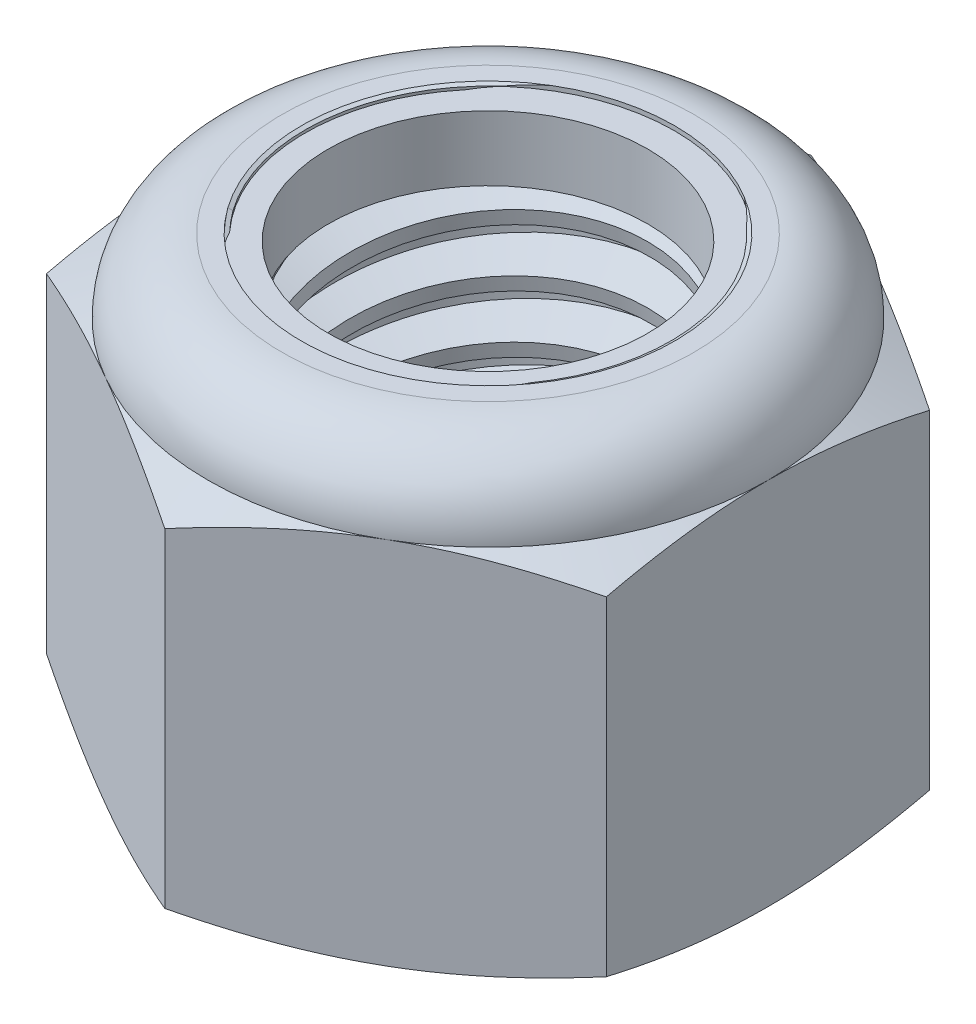
SolidWorks part; units mm, degrees
material "Plain Carbon Steel"
ref_plane "Front" through (0, 0, 0) normal (0, 0, 1) x (1, 0, 0)
ref_plane "Top" through (0, 0, 0) normal (0, 1, 0) x (1, 0, 0)
ref_plane "Right" through (0, 0, 0) normal (1, 0, 0) x (0, 0, -1)
sketch "Sketch1" plane through (0, 0, 0) normal (0, 1, 0) x (1, 0, 0)
  line L1 (0, 10.9985) -> (-9.525, 5.4993)
  line L2 (-9.525, 5.4993) -> (-9.525, -5.4993)
  line L3 (-9.525, -5.4993) -> (0, -10.9985)
  line L4 (0, -10.9985) -> (9.525, -5.4993)
  line L5 (9.525, -5.4993) -> (9.525, 5.4993)
  line L6 (9.525, 5.4993) -> (0, 10.9985)
  circle A0 centre (0, 0) radius 9.525 construction
  dimension "Hex Flats" = 19.05
extrude "Extrude1" add sketch "Sketch1" along normal blind 15.0812
sketch "Sketch2" plane through (0, 0, 0) normal (1, 0, 0) x (0, 0, -1)
  line L0 (-6.35, 0) -> (-6.35, 15.0812) construction
  line L1 (0, 0) -> (6.35, 0)
  line L2 (0, 0) -> (0, 15.0812)
  line L3 (0, 15.0812) -> (6.35, 15.0812)
  line L4 (6.35, 0) -> (6.35, 15.0812)
  line L5 (-5.4993, 15.0812) -> (5.4993, 15.0812) construction
  line L7 (0, -6.35) -> (0, 0) construction
  dimension "Thread Dia" = 12.7
revolve "Revolve1" add sketch "Sketch2" angle 360 about L7
sketch "Sketch3" plane through (0, 0, 0) normal (1, 0, 0) x (0, 0, -1)
  line L0 (6.35, 15.0813) -> (-6.35, 15.0813) construction
  line L1 (-6.35, 15.0813) -> (-6.35, 13.1274) construction
  line L2 (-6.35, 13.1274) -> (6.35, 15.0813) construction
  line L3 (6.35, 15.0813) -> (6.3871, 14.8399) construction
  line L4 (6.3871, 14.8399) -> (6.6471, 13.1501)
  line L5 (6.6471, 13.1501) -> (5.509, 13.5928)
  line L6 (5.509, 13.5928) -> (5.4347, 14.0756)
  line L7 (5.4347, 14.0756) -> (6.3871, 14.8399)
  line L8 (5.4719, 13.8342) -> (6.5171, 13.995) construction
  line L9 (6.35, 15.0813) -> (6.35, 13.9693) construction
  line L10 (6.35, 13.9693) -> (-6.35, 12.0154) construction
  line L11 (-6.35, 12.0154) -> (-6.35, 13.1274) construction
  line L12 (-0.3214, 15.0813) -> (0.3214, 10.9035) construction
  line L13 (-6.35, 0) -> (-6.35, 15.0812) construction
  line L14 (0, 15.0812) -> (6.35, 15.0812) construction
  line L15 (6.35, 0) -> (6.35, 15.0812) construction
  point P13 (0, 12.9924)
  dimension "D1" = 0.2442
  dimension "D2" = 0.4885
  dimension "Thread Pitch" = 1.9538
  dimension "D4" = 60
  dimension "D5" = 1.9538
revolve "Cut-Revolve1" cut sketch "Sketch3" angle 360 about L12
pattern_linear "LPattern1" count 8 spacing 1.9538 along (0, -1, 0) count 2 spacing 1.9538 along (0, 1, 0) of "Cut-Revolve1"
sketch "Sketch4" plane through (0, 0, 0) normal (1, 0, 0) x (0, 0, -1)
  line L0 (0, 15.0812) -> (6.35, 15.0812)
  line L1 (6.35, 15.0812) -> (5.4347, 14.6545)
  line L2 (5.4347, 14.6545) -> (5.4347, 0.4268)
  line L3 (5.4347, 0.4268) -> (6.35, 0)
  line L4 (6.35, 0) -> (0, 0)
  line L5 (0, 0) -> (0, 15.0812)
  line L6 (6.35, 0) -> (6.35, 15.0812) construction
  line L7 (0, 15.0812) -> (6.35, 15.0812) construction
  line L8 (0, 0) -> (6.35, 0) construction
  line L9 (0, 0) -> (0, 15.0812) construction
  line L10 (0, 15.0812) -> (0, 16.0911) construction
  dimension "D1" = 25
revolve "Cut-Revolve2" cut sketch "Sketch4" angle 360 about L10
combine bodies "Combine1" operation type subtract main body 112 bodies to subtract 111
sketch "Sketch5" plane through (0, 0, 0) normal (1, 0, 0) x (0, 0, -1)
  line L0 (0, 0) -> (9.525, 0)
  line L1 (9.525, 0) -> (10.9985, 0.6871)
  line L2 (10.9985, 0.6871) -> (10.9985, 11.8806)
  line L3 (10.9985, 11.8806) -> (9.525, 12.5677)
  line L4 (7.0115, 15.0812) -> (7.0115, 16.3512)
  line L5 (7.0115, 16.3512) -> (12.2685, 16.3512)
  line L6 (12.2685, 16.3512) -> (12.2685, -1.27)
  line L7 (12.2685, -1.27) -> (0, -1.27)
  line L8 (0, -1.27) -> (0, 0)
  line L9 (9.525, 12.5677) -> (9.525, 0) construction
  line L10 (0, 0) -> (6.35, 0) construction
  line L13 (10.9985, 6.2839) -> (12.2685, 6.2839) construction
  line L14 (10.9985, 15.0812) -> (10.9985, 0) construction
  line L15 (0, 0) -> (0, 16.3512) construction
  line L20 (0, 16.3512) -> (7.0115, 16.3512) construction
  line L22 (0, 15.0812) -> (6.35, 15.0812) construction
  arc A0 (9.525, 12.5677) -> (7.0115, 15.0812) centre (7.0115, 12.5677) ccw
  dimension "D1" = 25
  dimension "D2" = 1.27
  dimension "D3" = 15.0812
  dimension "D4" = 2.5135
revolve "Cut-Revolve3" cut sketch "Sketch5" angle 360 about L15
sketch "Sketch6" plane through (0, 0, 0) normal (1, 0, 0) x (0, 0, -1)
  line L0 (0, 12.5677) -> (9.3726, 12.5677)
  line L1 (7.0115, 14.9289) -> (6.2231, 14.9289)
  line L2 (0, 16.3512) -> (0, 12.5677)
  line L3 (6.2231, 16.3512) -> (0, 16.3512)
  line L4 (0, 16.3512) -> (7.0115, 16.3512) construction
  line L5 (0, 0) -> (0, 16.3512) construction
  line L6 (0, 16.3512) -> (0, 44.323) construction
  line L7 (6.2231, 14.9289) -> (6.2231, 16.3512)
  line L8 (7.0115, 15.0812) -> (7.0115, 14.9289) construction
  line L9 (6.2231, 14.9289) -> (5.4347, 14.9289) construction
  line L10 (5.4347, 14.9289) -> (5.4347, 14.6545) construction
  arc A0 (9.3726, 12.5677) -> (7.0115, 14.9289) centre (7.0115, 12.5677) ccw
  arc A1 (9.525, 12.5677) -> (7.0115, 15.0812) centre (7.0115, 12.5677) ccw construction
  dimension "D1" = 0.1524
revolve "Cut-Revolve4" cut sketch "Sketch6" angle 360 about L6
sketch "Sketch7" plane through (0, 0, 0) normal (1, 0, 0) x (0, 0, -1)
  line L0 (5.4347, 12.6439) -> (9.2951, 12.6439)
  line L1 (7.0115, 14.8527) -> (5.4347, 14.8527)
  line L2 (5.4347, 14.8527) -> (5.4347, 12.6439)
  line L3 (5.4347, 12.6439) -> (0, 12.6439) construction
  line L4 (0, 12.6439) -> (0, 14.8527) construction
  line L5 (0, 14.8527) -> (5.4347, 14.8527) construction
  line L6 (5.4347, 12.6439) -> (5.4347, 12.5677) construction
  line L7 (0, 12.5677) -> (9.3726, 12.5677) construction
  line L8 (7.0115, 14.8527) -> (7.0115, 14.9289) construction
  arc A0 (9.2951, 12.6439) -> (7.0115, 14.8527) centre (7.0115, 12.5677) ccw
  arc A2 (9.3726, 12.5677) -> (7.0115, 14.9289) centre (7.0115, 12.5677) ccw construction
  dimension "D1" = 0.0762
revolve "Revolve2" add sketch "Sketch7" angle 360 about L4
equation "\"D1@Sketch3\"=\"Thread Pitch@Sketch3\"/8"
equation "\"D2@Sketch3\"=\"Thread Pitch@Sketch3\"/4"
equation "\"D5@Sketch3\"=\"Thread Pitch@Sketch3\""
equation "\"D4@LPattern1\"=\"Thread Pitch@Sketch3\""
equation "\"D3@LPattern1\"=\"Thread Pitch@Sketch3\""
equation "\"D1@LPattern1\"=\"Height@Extrude1\"/\"Thread Pitch@Sketch3\""
equation "\"D4@Sketch5\"=\"Height@Extrude1\"/6"
